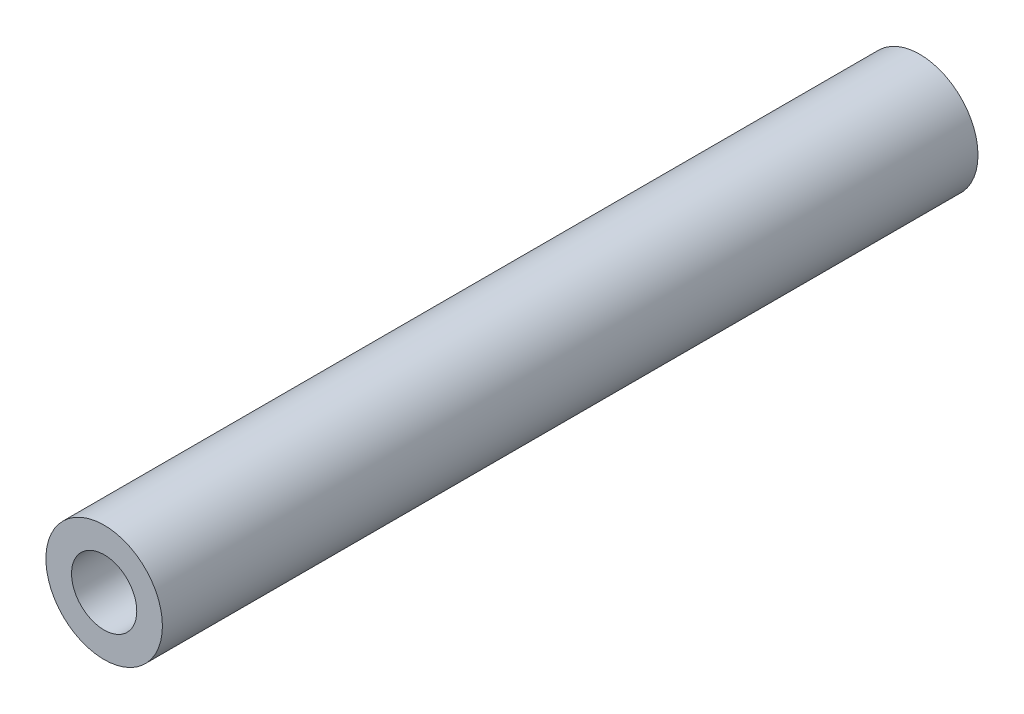
SolidWorks part; units mm, degrees
material "Copper"
ref_plane "Front Plane" through (0, 0, 0) normal (0, 0, 1) x (1, 0, 0)
ref_plane "Top Plane" through (0, 0, 0) normal (0, 1, 0) x (1, 0, 0)
ref_plane "Right Plane" through (0, 0, 0) normal (1, 0, 0) x (0, 0, -1)
sketch "Sketch1" plane through (0, 0, 0) normal (0, 0, 1) x (1, 0, 0)
  circle A0 centre (0, 0) radius 3.175
  circle A1 centre (0, 0) radius 1.778
  dimension "D1" = 3.556
  dimension "D2" = 6.35
extrude "Boss-Extrude1" add sketch "Sketch1" along normal blind 44.45
